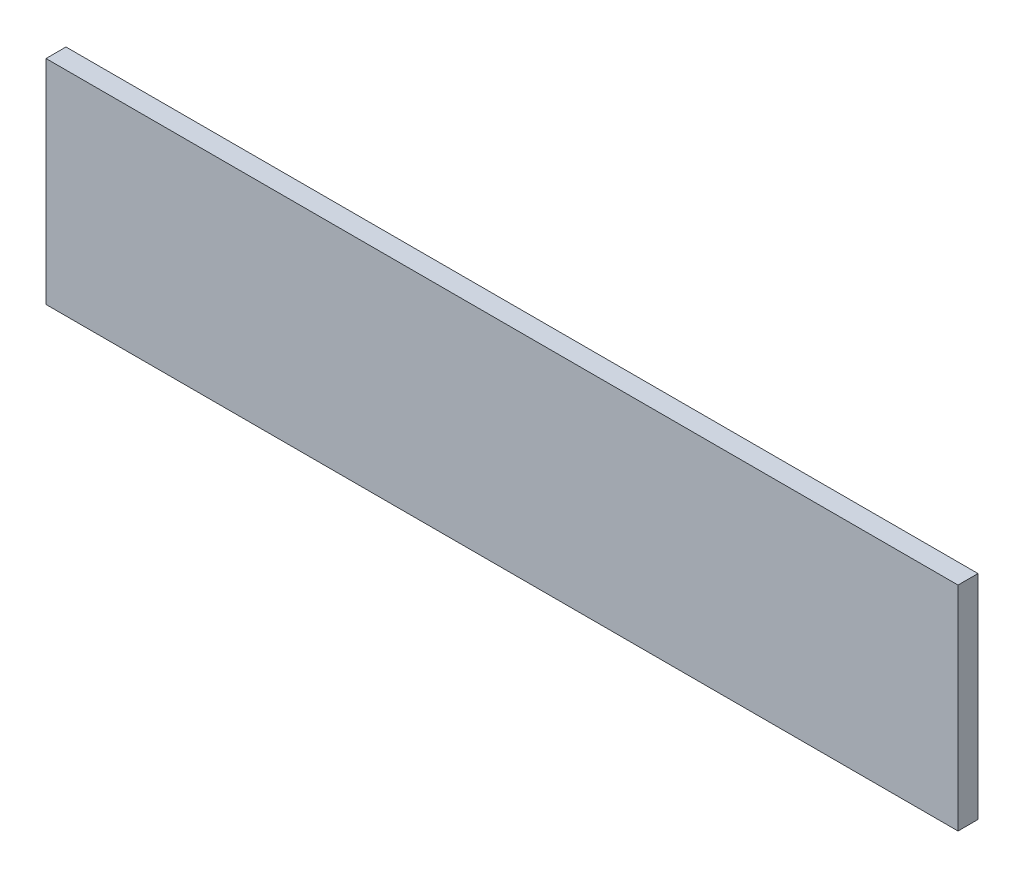
SolidWorks part; units mm, degrees
material "Oak"
ref_plane "Front Plane" through (0, 0, 0) normal (0, 0, 1) x (1, 0, 0)
ref_plane "Top Plane" through (0, 0, 0) normal (0, 1, 0) x (1, 0, 0)
ref_plane "Right Plane" through (0, 0, 0) normal (1, 0, 0) x (0, 0, -1)
sketch "Sketch1" plane through (0, 0, 0) normal (0, 0, 1) x (1, 0, 0)
  line L1 (-434.975, -101.6) -> (434.975, -101.6)
  line L2 (-434.975, -101.6) -> (-434.975, 101.6)
  line L3 (-434.975, 101.6) -> (434.975, 101.6)
  line L4 (434.975, -101.6) -> (434.975, 101.6)
  line L5 (-434.975, -101.6) -> (434.975, 101.6) construction
  line L6 (-434.975, 101.6) -> (434.975, -101.6) construction
  point P1 (0, 0)
  dimension "D1" = 869.95
  dimension "D2" = 203.2
extrude "Boss-Extrude1" add sketch "Sketch1" along normal blind 19.05
